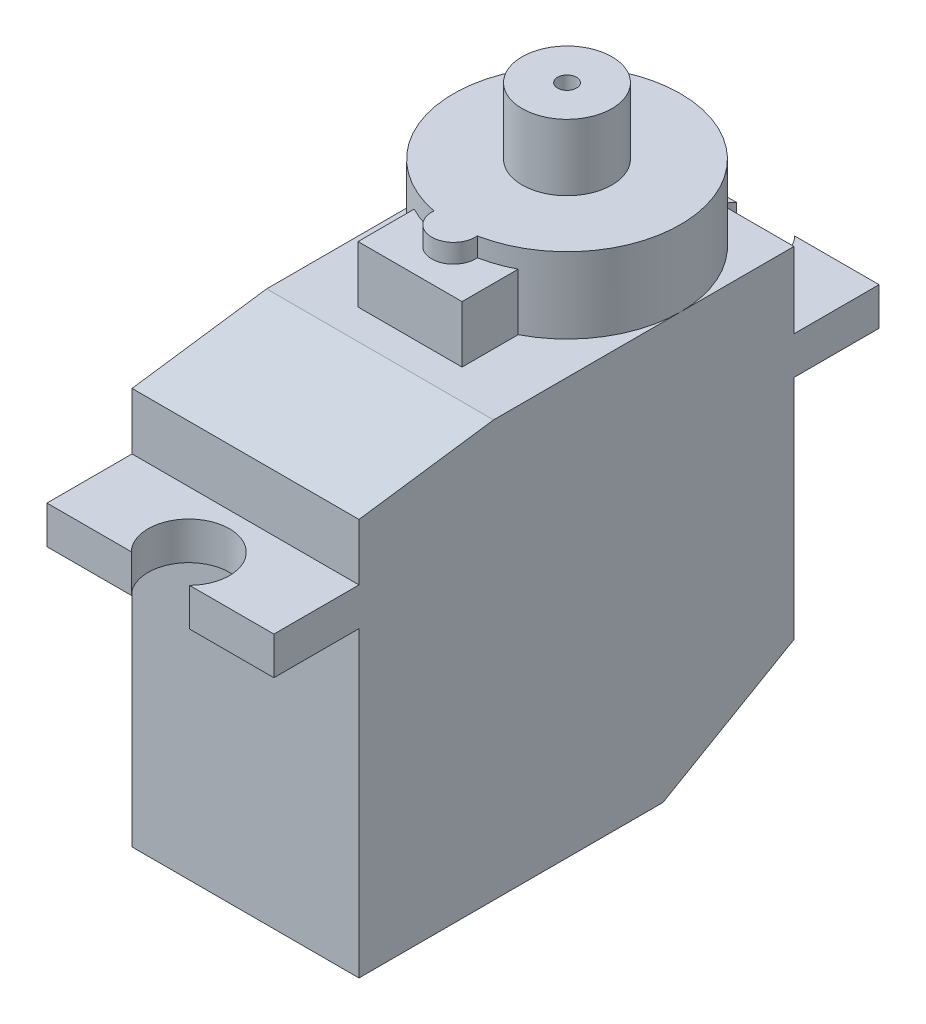
SolidWorks part; units mm, degrees
ref_plane "Front Plane" through (0, 0, 0) normal (0, 0, 1) x (1, 0, 0)
ref_plane "Top Plane" through (0, 0, 0) normal (0, 1, 0) x (1, 0, 0)
ref_plane "Right Plane" through (0, 0, 0) normal (1, 0, 0) x (0, 0, -1)
sketch "Sketch1" plane through (0, 0, 0) normal (0, 1, 0) x (1, 0, 0)
  line L0 (0, 6) -> (0, 0) construction
  line L1 (-6, 6) -> (6, 6)
  line L2 (-6, 6) -> (-6, -17)
  line L3 (-6, -17) -> (6, -17)
  line L4 (6, 6) -> (6, -17)
  dimension "D1" = 12
  dimension "D2" = 6
  dimension "D3" = 23
extrude "Boss-Extrude1" add sketch "Sketch1" along normal blind 22
chamfer "Chamfer1" distance 4 angle 60 1 edges at (0, 0, -6)
ref_plane "Plane1" through (0, 16, 0) normal (0, 1, 0) x (-1, 0, 0)
sketch "Sketch2" plane through (0, 16, 0) normal (0, 1, 0) x (-1, 0, 0)
  line L0 (6, -6) -> (6, -10.5)
  line L1 (6, -10.5) -> (1.5403, -10.5)
  line L2 (6, -6) -> (-6, -6)
  line L3 (-6, -6) -> (-6, -10.5)
  line L4 (-6, -10.5) -> (-1.5403, -10.5)
  line L5 (6, 5.5) -> (-6, 5.5) construction
  line L6 (6, -6) -> (6, 17) construction
  line L7 (-6, 17) -> (-6, -6) construction
  line L8 (-6, 21.5) -> (-1.5403, 21.5)
  line L9 (-6, 17) -> (-6, 21.5)
  line L10 (6, 17) -> (-6, 17)
  line L11 (6, 21.5) -> (1.5403, 21.5)
  line L12 (6, 17) -> (6, 21.5)
  arc A0 (1.5403, -10.5) -> (-1.5403, -10.5) centre (0, -9) ccw
  arc A1 (1.5403, 21.5) -> (-1.5403, 21.5) centre (0, 20) cw
  dimension "D1" = 2.15
  dimension "D2" = 4.5
  dimension "D3" = 3
extrude "Boss-Extrude2" add sketch "Sketch2" along normal blind 2
sketch "Sketch3" plane through (0, 22, 0) normal (0, 1, 0) x (1, 0, 0)
  line L0 (-6, 6) -> (-6, -17) construction
  circle A0 centre (0, 0) radius 6
extrude "Boss-Extrude3" add sketch "Sketch3" along normal blind 4
sketch "Sketch4" plane through (0, 22, 0) normal (0, 1, 0) x (1, 0, 0)
  line L1 (-2.75, -8.3) -> (2.75, -8.3)
  line L2 (-2.75, -8.3) -> (-2.75, 0)
  line L3 (-2.75, 0) -> (2.75, 0)
  line L4 (2.75, -8.3) -> (2.75, 0)
  dimension "D1" = 5.5
  dimension "D2" = 8.3
extrude "Boss-Extrude4" add sketch "Sketch4" along normal blind 3
sketch "Sketch5" plane through (0, 25, 0) normal (0, 1, 0) x (1, 0, 0)
  line L0 (0, -6) -> (0, 0) construction
  circle A0 centre (0, -6) radius 1.15
  arc A1 (-2.75, -5.3327) -> (2.75, -5.3327) centre (0, 0) ccw construction
  dimension "D1" = 2.3
extrude "Boss-Extrude5" add sketch "Sketch5" along normal up to surface (1 mm away) up to face at (0, 26, 6)
sketch "Sketch6" plane through (0, 26, 0) normal (0, 1, 0) x (1, 0, 0)
  circle A0 centre (0, 0) radius 2.375
  circle A1 centre (0, 0) radius 0.5
  dimension "D1" = 4.75
  dimension "D2" = 1
extrude "Boss-Extrude6" add sketch "Sketch6" along normal blind 3.5
chamfer "Chamfer2" distance 1 angle 82 1 edges at (0, 22, 17)
